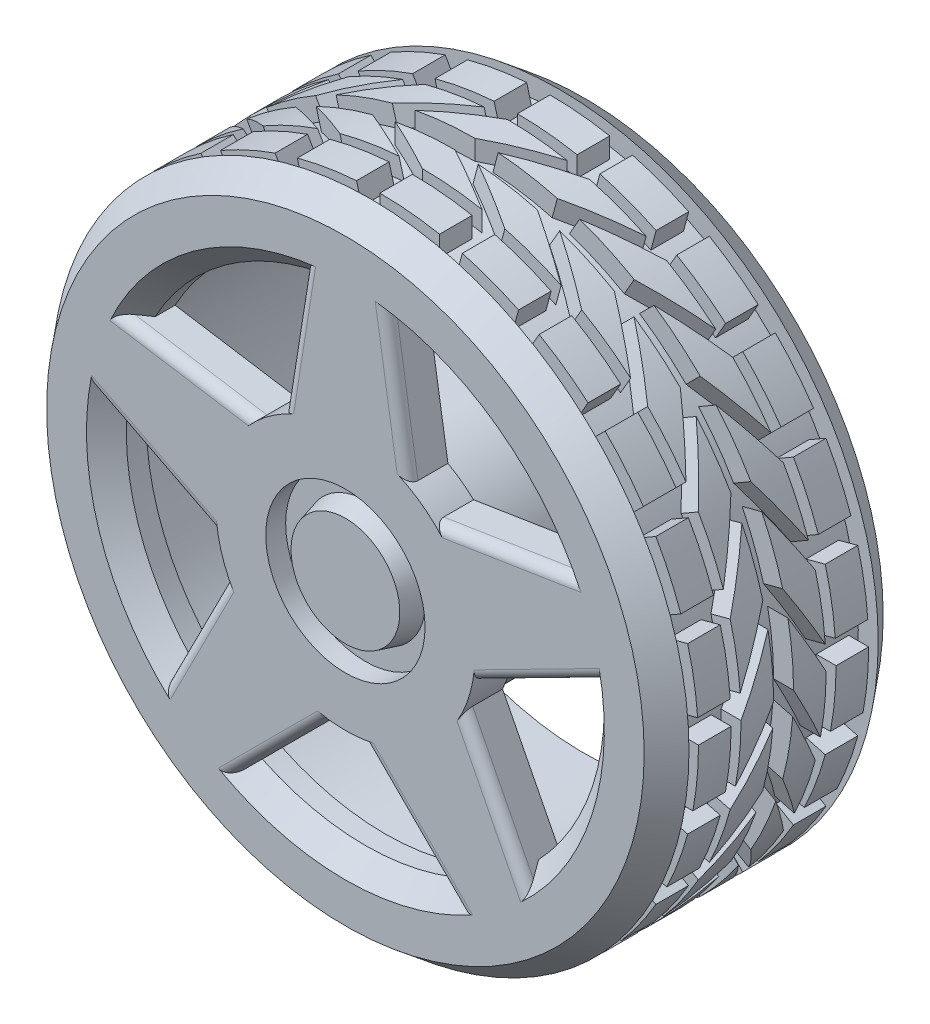
SolidWorks part; units mm, degrees
ref_plane "Front Plane" through (0, 0, 0) normal (0, 0, 1) x (1, 0, 0)
ref_plane "Top Plane" through (0, 0, 0) normal (0, 1, 0) x (1, 0, 0)
ref_plane "Right Plane" through (0, 0, 0) normal (1, 0, 0) x (0, 0, -1)
sketch "Sketch1" plane through (0, 0, 0) normal (1, 0, 0) x (0, 0, -1)
  line L21 (-38.1, 0) -> (0, 0) construction
  line L38 (38.1, 95.25) -> (38.1, 25.4)
  line L40 (-30.1625, 95.25) -> (30.1625, 95.25)
  line L41 (-38.1, 95.25) -> (-38.1, 82.55)
  line L42 (-30.1625, 101.6) -> (-38.1, 95.25)
  line L43 (38.1, 95.25) -> (30.1625, 101.6)
  line L44 (30.1625, 101.6) -> (30.1625, 95.25)
  line L45 (-30.1625, 95.25) -> (-30.1625, 101.6)
  line L46 (38.1, 25.4) -> (-19.05, 25.4)
  line L48 (-31.75, 25.4) -> (-31.75, 76.2)
  line L49 (-31.75, 76.2) -> (-38.1, 82.55)
  line L50 (-31.75, 25.4) -> (-31.75, 0)
  line L51 (-31.75, 0) -> (-19.05, 0)
  line L52 (-19.05, 0) -> (-19.05, 25.4)
  dimension "D2" = 25.4
  dimension "D3" = 12.7
  dimension "D4" = 50.8
  dimension "D10" = 6.35
revolve "Revolve2" add sketch "Sketch1" angle 360 about L21
ref_plane "Plane1" through (101.6, 0, 0) normal (1, 0, 0) x (0, 0, -1)
sketch "Sketch2" plane through (101.6, 0, 0) normal (1, 0, 0) x (0, 0, -1)
  line L0 (0, 0) -> (-3.175, 0)
  line L1 (-3.175, 0) -> (-3.175, 19.05)
  line L2 (0, 24.2705) -> (0, -24.6051) construction
  line L3 (30.1625, 0) -> (-30.1625, 0) construction
  line L4 (-27.1221, 0) -> (-27.1221, -19.05)
  line L5 (-27.1221, -19.05) -> (-16.736, -19.05)
  line L6 (-27.1221, 0) -> (-16.736, 0)
  line L7 (-13.561, 0) -> (-3.175, 19.05)
  line L8 (-13.561, -19.05) -> (-3.175, 0)
  line L9 (-16.736, 0) -> (-16.736, -19.05)
  line L10 (-13.561, -19.05) -> (-13.561, 0)
  line L11 (13.561, -19.05) -> (3.175, 0)
  line L12 (13.561, -19.05) -> (13.561, 0)
  line L13 (13.561, 0) -> (3.175, 19.05)
  line L14 (3.175, 0) -> (3.175, 19.05)
  line L15 (27.1221, 0) -> (16.736, 0)
  line L16 (16.736, 0) -> (16.736, -19.05)
  line L17 (27.1221, -19.05) -> (16.736, -19.05)
  line L18 (27.1221, 0) -> (27.1221, -19.05)
  point P6 (-3.175, 0)
  dimension "D1" = 3.175
  dimension "D2" = 19.05
  dimension "D4" = 19.05
  dimension "D5" = 151.401
  dimension "D6" = 3.175
  dimension "D7" = 10.386
  dimension "D8" = 270
extrude "Boss-Extrude1" add sketch "Sketch2" against normal blind 9.525 contours L9 L6 L4 L5 | L10 L8 L1 L7 | L18 L15 L16 L17 | L14 L11 L12 L13
pattern_circular "CirPattern1" count 24 every 15 about axis through (0, 0, 0) along (0, 0, 1) of "Boss-Extrude1"
sketch "Sketch3" plane through (0, 0, -38.1) normal (0, 0, -1) x (-1, 0, 0)
  circle A0 centre (0, 0) radius 85.725
  circle A1 centre (0, 0) radius 38.1
  dimension "D1" = 171.45
  dimension "D2" = 76.2
extrude "Cut-Extrude1" cut sketch "Sketch3" against normal blind 63.5
sketch "Sketch4" plane through (0, 0, 38.1) normal (0, 0, 1) x (1, 0, 0)
  circle A0 centre (0, 0) radius 101.6
  circle A1 centre (0, 0) radius 103.3705
extrude "Cut-Extrude2" cut sketch "Sketch4" against normal up to surface (76.2 mm away) up to face at (-85.725, 0, -38.1)
sketch "Sketch5" plane through (0, 0, 38.1) normal (0, 0, 1) x (1, 0, 0)
  line L0 (0, 0) -> (0, 82.55) construction
  line L1 (19.9859, 36.1136) -> (12.7824, 81.5544)
  line L2 (-19.9859, 36.1136) -> (-12.7824, 81.5544)
  line L3 (28.1701, 30.1674) -> (73.6128, 37.3585)
  line L4 (40.522, -7.848) -> (81.5128, 13.0449)
  line L5 (37.3959, -17.4691) -> (58.2776, -58.4655)
  line L6 (5.0581, -40.9639) -> (37.5953, -73.4922)
  line L7 (-5.0581, -40.9639) -> (-37.5953, -73.4922)
  line L8 (-37.3959, -17.4691) -> (-58.2776, -58.4655)
  line L9 (-40.522, -7.848) -> (-81.5128, 13.0449)
  line L10 (-28.1701, 30.1674) -> (-73.6128, 37.3585)
  arc A0 (-73.6128, 37.3585) -> (-81.5128, 13.0449) centre (0, 0) ccw
  arc A1 (-5.0581, -40.9639) -> (5.0581, -40.9639) centre (0, 0) ccw
  arc A2 (12.7824, 81.5544) -> (-12.7824, 81.5544) centre (0, 0) ccw
  arc A3 (-58.2776, -58.4655) -> (-37.5953, -73.4922) centre (0, 0) ccw
  arc A4 (37.5953, -73.4922) -> (58.2776, -58.4655) centre (0, 0) ccw
  arc A5 (81.5128, 13.0449) -> (73.6128, 37.3585) centre (0, 0) ccw
  arc A6 (37.3959, -17.4691) -> (40.522, -7.848) centre (0, 0) ccw
  arc A7 (-40.522, -7.848) -> (-37.3959, -17.4691) centre (0, 0) ccw
  arc A8 (28.1701, 30.1674) -> (19.9859, 36.1136) centre (0, 0) ccw
  arc A9 (-19.9859, 36.1136) -> (-28.1701, 30.1674) centre (0, 0) ccw
  circle A10 centre (0, 0) radius 25.4
  point P28 (0, 0)
  dimension "D1" = 82.55
  dimension "D3" = 50.8
  dimension "D2" = 5
extrude "Boss-Extrude2" add sketch "Sketch5" against normal up to surface (6.35 mm away)
sketch "Sketch6" plane through (0, 0, 31.75) normal (0, 0, 1) x (1, 0, 0)
  line L0 (28.1701, 30.1674) -> (66.9923, 36.3108) construction
  line L1 (13.8319, 74.9341) -> (19.9859, 36.1136) construction
  line L2 (75.5408, 10.001) -> (40.522, -7.848) construction
  line L3 (37.3959, -17.4691) -> (55.2354, -52.4928) construction
  line L4 (32.8549, -68.7531) -> (5.0581, -40.9639) construction
  line L5 (-5.0581, -40.9639) -> (-32.8549, -68.7531) construction
  line L6 (-55.2354, -52.4928) -> (-37.3959, -17.4691) construction
  line L7 (-40.522, -7.848) -> (-75.5408, 10.001) construction
  line L8 (-66.9923, 36.3108) -> (-28.1701, 30.1674) construction
  line L9 (-19.9859, 36.1136) -> (-13.8319, 74.9341) construction
  line L10 (28.1701, 30.1674) -> (66.9923, 36.3108)
  line L11 (13.8319, 74.9341) -> (19.9859, 36.1136)
  line L12 (75.5408, 10.001) -> (40.522, -7.848)
  line L13 (37.3959, -17.4691) -> (55.2354, -52.4928)
  line L14 (32.8549, -68.7531) -> (5.0581, -40.9639)
  line L15 (-5.0581, -40.9639) -> (-32.8549, -68.7531)
  line L16 (-55.2354, -52.4928) -> (-37.3959, -17.4691)
  line L17 (-40.522, -7.848) -> (-75.5408, 10.001)
  line L18 (-66.9923, 36.3108) -> (-28.1701, 30.1674)
  line L19 (-19.9859, 36.1136) -> (-13.8319, 74.9341)
  arc A0 (28.1701, 30.1674) -> (19.9859, 36.1136) centre (0, 0) ccw construction
  arc A1 (66.9923, 36.3108) -> (13.8319, 74.9341) centre (0, 0) ccw construction
  arc A2 (55.2354, -52.4928) -> (75.5408, 10.001) centre (0, 0) ccw construction
  arc A3 (37.3959, -17.4691) -> (40.522, -7.848) centre (0, 0) ccw construction
  arc A4 (-32.8549, -68.7531) -> (32.8549, -68.7531) centre (0, 0) ccw construction
  arc A5 (-5.0581, -40.9639) -> (5.0581, -40.9639) centre (0, 0) ccw construction
  arc A6 (-75.5408, 10.001) -> (-55.2354, -52.4928) centre (0, 0) ccw construction
  arc A7 (-40.522, -7.848) -> (-37.3959, -17.4691) centre (0, 0) ccw construction
  arc A8 (-13.8319, 74.9341) -> (-66.9923, 36.3108) centre (0, 0) ccw construction
  arc A9 (-19.9859, 36.1136) -> (-28.1701, 30.1674) centre (0, 0) ccw construction
  arc A10 (28.1701, 30.1674) -> (19.9859, 36.1136) centre (0, 0) ccw
  arc A11 (66.9923, 36.3108) -> (13.8319, 74.9341) centre (0, 0) ccw
  arc A12 (55.2354, -52.4928) -> (75.5408, 10.001) centre (0, 0) ccw
  arc A13 (37.3959, -17.4691) -> (40.522, -7.848) centre (0, 0) ccw
  arc A14 (-32.8549, -68.7531) -> (32.8549, -68.7531) centre (0, 0) ccw
  arc A15 (-5.0581, -40.9639) -> (5.0581, -40.9639) centre (0, 0) ccw
  arc A16 (-75.5408, 10.001) -> (-55.2354, -52.4928) centre (0, 0) ccw
  arc A17 (-40.522, -7.848) -> (-37.3959, -17.4691) centre (0, 0) ccw
  arc A18 (-13.8319, 74.9341) -> (-66.9923, 36.3108) centre (0, 0) ccw
  arc A19 (-19.9859, 36.1136) -> (-28.1701, 30.1674) centre (0, 0) ccw
extrude "Cut-Extrude3" cut sketch "Sketch6" against normal up to surface (6.35 mm away) up to face at (-38.1, 0, 25.4)
fillet "Fillet1" radius 3.175 10 edges at (16.3841, 58.834, 38.1) (-16.3841, 58.834, 38.1) (50.8914, 33.7629, 38.1) (61.0174, 2.5984, 38.1) (47.8368, -37.9673, 38.1) (21.3267, -57.228, 38.1) (-21.3267, -57.228, 38.1) (-47.8368, -37.9673, 38.1) (-61.0174, 2.5984, 38.1) (-50.8914, 33.7629, 38.1)
sketch "Sketch7" plane through (0, 0, 31.75) normal (0, 0, 1) x (1, 0, 0)
  circle A0 centre (0, 0) radius 19.05
  dimension "D1" = 38.1
extrude "Boss-Extrude3" add sketch "Sketch7" along normal up to surface (6.35 mm away) draft 15
